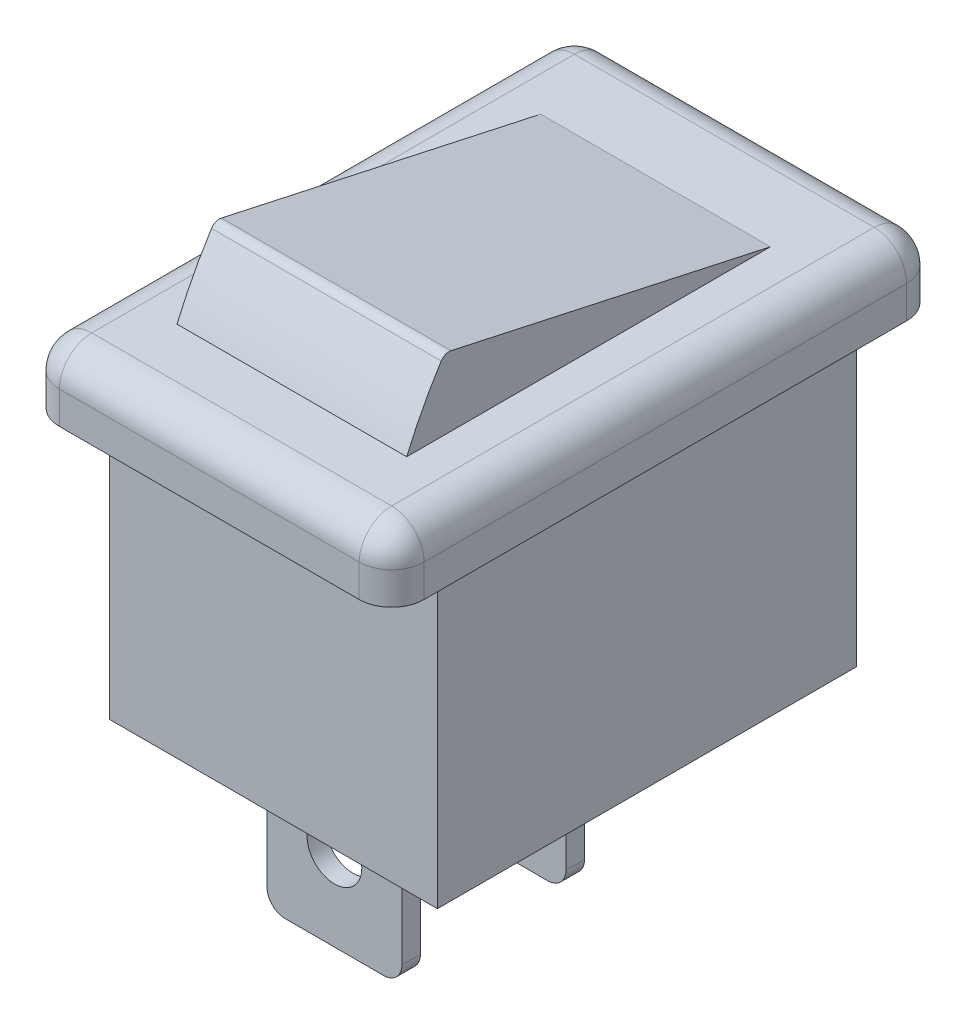
SolidWorks part; units mm, degrees
ref_plane "Front" through (0, 0, 0) normal (0, 0, 1) x (1, 0, 0)
ref_plane "Top" through (0, 0, 0) normal (0, 1, 0) x (1, 0, 0)
ref_plane "Right" through (0, 0, 0) normal (1, 0, 0) x (0, 0, -1)
sketch "Sketch1" plane through (0, 0, 0) normal (1, 0, 0) x (0, 0, -1)
  line L0 (-5.75, 0) -> (5.75, 0) construction
  line L1 (-5.75, 0) -> (5.75, 0) construction
  line L2 (-5.75, 0) -> (-5.75, -8.0264)
  line L3 (-5.75, -8.0264) -> (5.75, -8.0264)
  line L4 (5.75, 0) -> (5.75, -8.0264)
  line L5 (-7.5057, 1.778) -> (7.5057, 1.778)
  line L6 (-7.5057, 1.778) -> (-7.5057, 0)
  line L7 (-7.5057, 0) -> (-5.75, 0)
  line L8 (7.5057, 1.778) -> (7.5057, 0)
  line L9 (5.75, 0) -> (7.5057, 0)
  dimension "D1" = 15.0114
  dimension "D2" = 11.5
  dimension "D3" = 9.8044
  dimension "D4" = 1.778
extrude "Boss-Extrude1" add sketch "Sketch1" along normal mid plane 9
sketch "Sketch2" plane through (0, 1.778, 0) normal (0, 1, 0) x (1, 0, 0)
  line L0 (4.5, 7.5057) -> (-4.5, 7.5057) construction
  line L1 (-5, -7.5057) -> (5, -7.5057)
  line L2 (-5, -7.5057) -> (-5, 7.5057)
  line L3 (-5, 7.5057) -> (5, 7.5057)
  line L4 (5, -7.5057) -> (5, 7.5057)
  line L5 (-5, -7.5057) -> (5, 7.5057) construction
  line L6 (-5, 7.5057) -> (5, -7.5057) construction
  point P0 (0, 0)
  dimension "D1" = 10
extrude "Boss-Extrude2" add sketch "Sketch2" against normal up to surface (1.778 mm away) up to face at (0, 0, 6.6278)
fillet "Fillet1" radius 0.889 8 edges at (5, 1.778, 0) (0, 1.778, 7.5057) (-5, 1.778, 0) (0, 1.778, -7.5057) (-5, 0.889, -7.5057) (-5, 0.889, 7.5057) (5, 0.889, -7.5057) (5, 0.889, 7.5057)
sketch "Sketch3" plane through (0, -8.0264, 0) normal (0, -1, 0) x (1, 0, 0)
  line L0 (0, 5.75) -> (0, -5.75) construction
  line L1 (4.5, 5.75) -> (-4.5, 5.75) construction
  line L2 (4.5, -5.75) -> (-4.5, -5.75) construction
  line L3 (4.5, -5.75) -> (-4.5, -5.75) construction
  line L4 (-1.85, 4.074) -> (1.85, 4.074)
  line L5 (-1.85, 4.074) -> (-1.85, 3.566)
  line L6 (-1.85, 3.566) -> (1.85, 3.566)
  line L7 (1.85, 4.074) -> (1.85, 3.566)
  line L8 (-1.85, 4.074) -> (1.85, 3.566) construction
  line L9 (-1.85, 3.566) -> (1.85, 4.074) construction
  line L10 (-1.85, -0.426) -> (1.85, -0.426)
  line L11 (-1.85, -0.426) -> (-1.85, -0.934)
  line L12 (-1.85, -0.934) -> (1.85, -0.934)
  line L13 (1.85, -0.426) -> (1.85, -0.934)
  line L14 (-1.85, -0.426) -> (1.85, -0.934) construction
  line L15 (-1.85, -0.934) -> (1.85, -0.426) construction
  point P6 (0, 3.82)
  point P11 (0, -0.68)
  dimension "D1" = 0.508
  dimension "D2" = 4.5
  dimension "D3" = 3.7
  dimension "D4" = 5.07
extrude "Boss-Extrude3" add sketch "Sketch3" along normal blind 4
fillet "Fillet2" radius 0.5 4 edges at (1.85, -12.0264, -0.68) (-1.85, -12.0264, -0.68) (1.85, -12.0264, 3.82) (-1.85, -12.0264, 3.82)
sketch "Sketch4" plane through (0, 0, 4.074) normal (0, 0, 1) x (1, 0, 0)
  line L0 (0, -8.0264) -> (0, -9.7764) construction
  line L1 (4.5, -8.0264) -> (-4.5, -8.0264) construction
  line L2 (0, -9.7764) -> (-1.85, -9.7764) construction
  line L3 (-1.85, -11.5264) -> (-1.85, -8.0264) construction
  circle A0 centre (0, -9.7764) radius 0.75
  dimension "D1" = 1.5
extrude "Cut-Extrude1" cut sketch "Sketch4" against normal through all
sketch "Sketch5" plane through (0, 0, 0) normal (1, 0, 0) x (0, 0, -1)
  line L0 (4.734, 1.778) -> (-4.028, 3.6905)
  line L1 (-6.6167, 1.778) -> (6.6167, 1.778) construction
  line L3 (-5.75, 0) -> (-5.75, -8.0264) construction
  line L4 (5.75, -8.0264) -> (5.75, 0) construction
  line L5 (-5.242, 1.778) -> (4.734, 1.778)
  arc A0 (-4.2963, 3.579) -> (-5.242, 1.778) centre (5.8521, -2.8986) ccw
  arc A1 (-4.028, 3.6905) -> (-4.2963, 3.579) centre (-4.0822, 3.4424) ccw
  point P12 (-4.1997, 3.728)
  dimension "D5" = 0.254
  dimension "D1" = 1.95
  dimension "D2" = 0.508
  dimension "D3" = 1.016
  dimension "D4" = 9.144
extrude "Boss-Extrude4" add sketch "Sketch5" along normal mid plane 6.3
